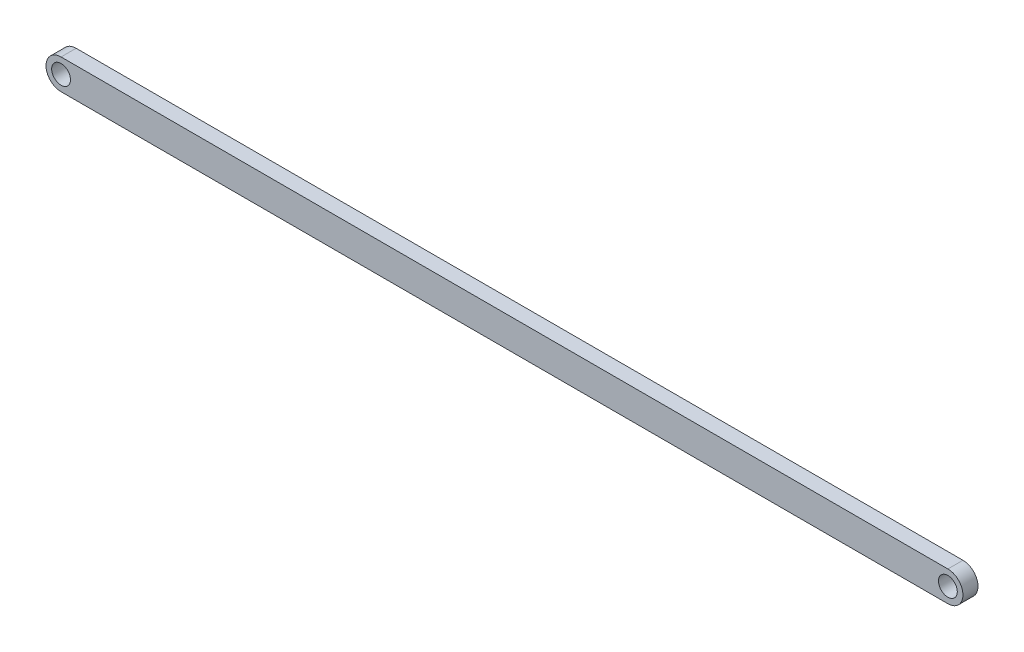
SolidWorks part; units mm, degrees
ref_plane "Front Plane" through (0, 0, 0) normal (0, 0, 1) x (1, 0, 0)
ref_plane "Top Plane" through (0, 0, 0) normal (0, 1, 0) x (1, 0, 0)
ref_plane "Right Plane" through (0, 0, 0) normal (1, 0, 0) x (0, 0, -1)
sketch "Sketch1" plane through (0, 0, 0) normal (0, 0, 1) x (1, 0, 0)
  line L1 (0, -3.175) -> (186.944, -3.175)
  line L3 (0, 3.175) -> (186.944, 3.175)
  circle A0 centre (0, 0) radius 1.9844
  circle A1 centre (186.944, 0) radius 1.9844
  arc A2 (0, 3.175) -> (0, -3.175) centre (0, 0) ccw
  arc A3 (186.944, -3.175) -> (186.944, 3.175) centre (186.944, 0) ccw
  dimension "D1" = 3.9688
  dimension "D2" = 3.9688
  dimension "D3" = 186.944
  dimension "D4" = 3.175
  dimension "D5" = 3.175
  dimension "D6" = 0
extrude "Boss-Extrude1" add sketch "Sketch1" along normal blind 3.175
